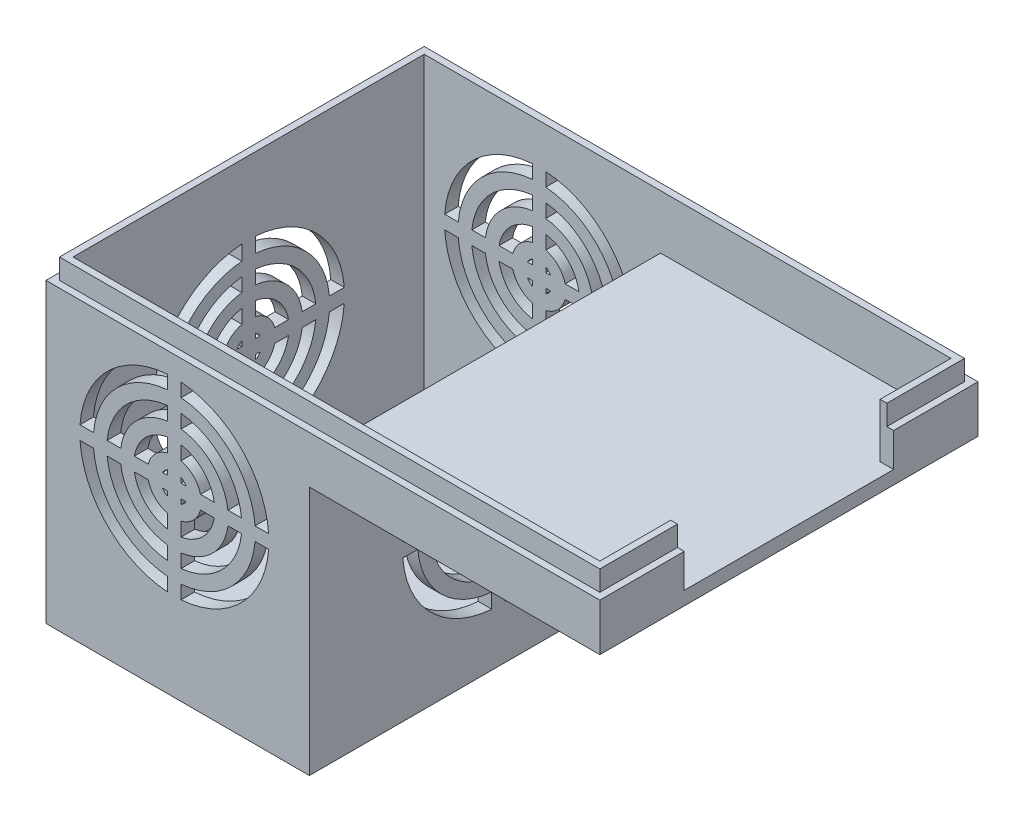
SolidWorks part; units mm, degrees
ref_plane "Front Plane" through (0, 0, 0) normal (0, 0, 1) x (1, 0, 0)
ref_plane "Top Plane" through (0, 0, 0) normal (0, 1, 0) x (1, 0, 0)
ref_plane "Right Plane" through (0, 0, 0) normal (1, 0, 0) x (0, 0, -1)
sketch "Sketch1" plane through (0, 0, 0) normal (0, 1, 0) x (1, 0, 0)
  line L1 (-41, -28) -> (41, -28)
  line L2 (-41, -28) -> (-41, 28)
  line L3 (-41, 28) -> (41, 28)
  line L4 (41, -28) -> (41, 28)
  line L5 (-41, -28) -> (41, 28) construction
  line L6 (-41, 28) -> (41, -28) construction
  point P0 (0, 0)
  dimension "D1" = 82
  dimension "D2" = 56
extrude "Boss-Extrude1" add sketch "Sketch1" along normal blind 47
sketch "Sketch2" plane through (0, 47, 0) normal (0, 1, 0) x (1, 0, 0)
  line L4 (40, -27) -> (40, 27)
  line L5 (40, 27) -> (-40, 27)
  line L6 (-40, 27) -> (-40, -27)
  line L7 (-40, -27) -> (40, -27)
  line L8 (41, -28) -> (41, 28)
  line L9 (41, 28) -> (-41, 28)
  line L10 (-41, 28) -> (-41, -28)
  line L11 (-41, -28) -> (41, -28)
  line L12 (41, -28) -> (41, 28)
  line L13 (41, 28) -> (-41, 28)
  line L14 (-41, 28) -> (-41, -28)
  line L15 (-41, -28) -> (41, -28)
  dimension "D1" = 0
  dimension "D2" = 1
extrude "Cut-Extrude1" cut sketch "Sketch2" against normal blind 3
sketch "Sketch3" plane through (0, 0, 28) normal (0, 0, 1) x (1, 0, 0)
  line L0 (-41, 44) -> (41, 44) construction
  line L1 (41, 0) -> (-2, 0)
  line L2 (41, 0) -> (41, 37)
  line L3 (41, 37) -> (-2, 37)
  line L4 (-2, 0) -> (-2, 37)
  dimension "D1" = 43
  dimension "D2" = 7
extrude "Cut-Extrude2" cut sketch "Sketch3" against normal blind 72 contours L2 L1 L4 L3
sketch3d "3DSketch2"
  line L0 (39, 47, -26) -> (-39, 47, -26)
  line L1 (-39, 47, -26) -> (-39, 47, 26)
  line L2 (-39, 47, 26) -> (39, 47, 26)
  line L3 (39, 47, 26) -> (39, 47, -26)
  line L4 (39, 47, -26) -> (-39, 47, -26)
  line L5 (-39, 47, -26) -> (-39, 47, 26)
  line L6 (-39, 47, 26) -> (39, 47, 26)
  line L7 (39, 47, 26) -> (39, 47, -26)
  dimension "D1" = 1
extrude "Cut-Extrude3" cut sketch "3DSketch2" along direction (0, -1, 0) on the side of the normal blind 8 contours L4 L5 L6 L7
sketch "Sketch4" plane through (0, 39, 0) normal (0, 1, 0) x (1, 0, 0)
  line L0 (-39, -26) -> (39, -26) construction
  line L1 (-39, 26) -> (-4, 26)
  line L2 (-39, 26) -> (-39, -26)
  line L3 (-39, -26) -> (-4, -26)
  line L4 (-4, 26) -> (-4, -26)
  dimension "D1" = 35
extrude "Cut-Extrude4" cut sketch "Sketch4" against normal blind 37
sketch "Sketch5" plane through (40, 0, 0) normal (1, 0, 0) x (0, 0, -1)
  line L0 (-27, 47) -> (27, 47) construction
  line L1 (-15.5, 55) -> (15.5, 55)
  line L2 (-15.5, 55) -> (-15.5, 39)
  line L3 (-15.5, 39) -> (15.5, 39)
  line L4 (15.5, 55) -> (15.5, 39)
  line L5 (-15.5, 55) -> (15.5, 39) construction
  line L6 (-15.5, 39) -> (15.5, 55) construction
  point P0 (0, 47)
  dimension "D1" = 31
  dimension "D2" = 16
extrude "Cut-Extrude5" cut sketch "Sketch5" against normal blind 11 and the other way blind 10
sketch "Sketch6" plane through (0, 0, -28) normal (0, 0, -1) x (-1, 0, 0)
  line L3 (8.0358, 28) -> (35.9642, 28)
  line L4 (35.9642, 26) -> (8.0358, 26)
  line L5 (21, 40.9642) -> (21, 13.0358)
  line L6 (23, 40.9642) -> (23, 13.0358)
  line L7 (-40, 47) -> (40, 47) construction
  line L8 (2, 0) -> (2, 37) construction
  circle A0 centre (22, 27) radius 2
  circle A1 centre (22, 27) radius 4
  circle A2 centre (22, 27) radius 6
  circle A3 centre (22, 27) radius 8
  circle A4 centre (22, 27) radius 10
  circle A5 centre (22, 27) radius 12
  circle A6 centre (22, 27) radius 14
  dimension "D1" = 4
  dimension "D2" = 8
  dimension "D3" = 12
  dimension "D4" = 16
  dimension "D5" = 20
  dimension "D6" = 24
  dimension "D7" = 28
  dimension "D8" = 20
  dimension "D9" = 20
extrude "Cut-Extrude6" cut sketch "Sketch6" against normal blind 108 contours L5 A6 L3 A5 | L4 A6 L5 A5 | L6 A6 L4 A5 | L3 A6 L6 A5 | L5 A4 L3 A3 | L4 A4 L5 A3 | L6 A4 L4 A3 | L3 A4 L6 A3 | L3 A2 L6 A1 | L4 A2 L5 A1 | L5 A2 L3 A1 | L6 A2 L4 A1 | L5 A0 L3 | L3 A0 L6 | L6 A0 L4 | L4 A0 L5
sketch "Sketch7" plane through (-41, 0, 0) normal (-1, 0, 0) x (0, 0, 1)
  line L0 (-27, 47) -> (27, 47) construction
  line L1 (-28, 44) -> (-28, 0) construction
  line L3 (-14.1635, 23.0165) -> (14.1635, 23.0165)
  line L4 (14.1635, 20.9835) -> (-14.1635, 20.9835)
  line L5 (-1, 36.1646) -> (-1, 7.8354)
  line L6 (1, 36.1646) -> (1, 7.8354)
  circle A0 centre (0, 22) radius 2
  circle A1 centre (0, 22) radius 4
  circle A2 centre (0, 22) radius 6
  circle A3 centre (0, 22) radius 8
  circle A4 centre (0, 22) radius 10
  circle A5 centre (0, 22) radius 12
  circle A6 centre (0, 22) radius 14.1999
  dimension "D1" = 28
  dimension "D2" = 1
  dimension "D3" = 1
  dimension "D4" = 25
extrude "Cut-Extrude7" cut sketch "Sketch7" against normal blind 63 contours L5 A6 L3 A5 | L4 A6 L5 A5 | L6 A6 L4 A5 | L3 A6 L6 A5 | L5 A4 L3 A3 | L4 A4 L5 A3 | L6 A4 L4 A3 | L3 A4 L6 A3 | L5 A2 L3 A1 | L4 A2 L5 A1 | L6 A2 L4 A1 | L3 A2 L6 A1 | L5 A0 L3 | L4 A0 L5 | L6 A0 L4 | L3 A0 L6
